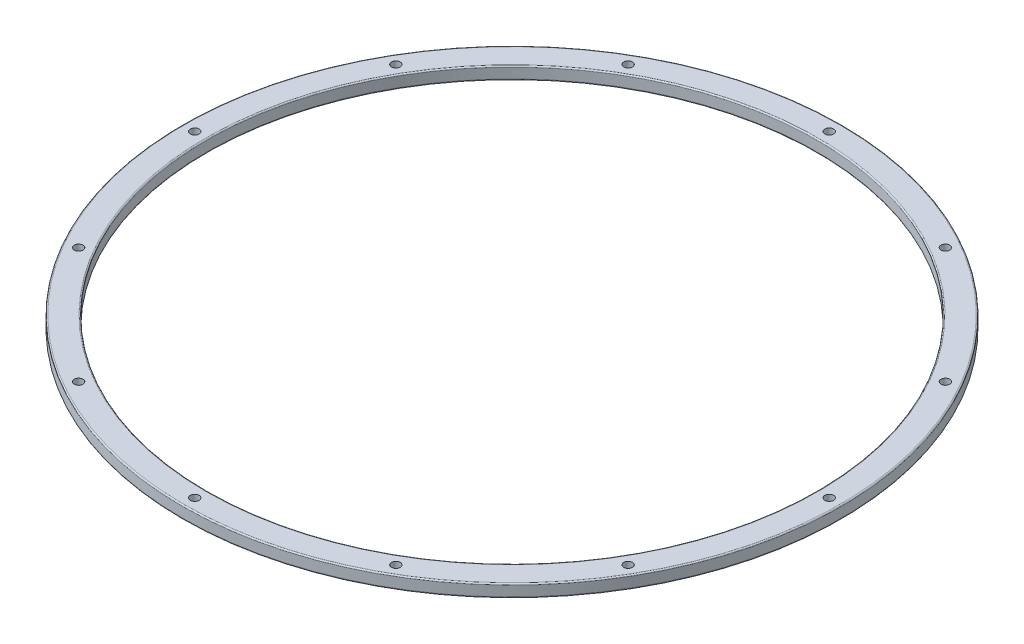
SolidWorks part; units mm, degrees
material "PTFE (general)"
ref_plane "Front Plane" through (0, 0, 0) normal (0, 0, 1) x (1, 0, 0)
ref_plane "Top Plane" through (0, 0, 0) normal (0, 1, 0) x (1, 0, 0)
ref_plane "Right Plane" through (0, 0, 0) normal (1, 0, 0) x (0, 0, -1)
ref_axis "Axis1" through (0, 55, 0) along (0, -1, 0)
sketch "Sketch1" plane through (0, 0, 0) normal (0, 0, 1) x (1, 0, 0)
  line L0 (-76.2, 0) -> (0, 0) construction
  line L1 (-76.5175, 0) -> (-82.042, 0)
  line L2 (-76.2, 0.3175) -> (-76.2, 2.8575)
  line L3 (-76.5175, 3.175) -> (-82.042, 3.175)
  line L4 (-82.3595, 0.3175) -> (-82.3595, 2.8575)
  line L5 (0, 55) -> (0, -55) construction
  arc A0 (-82.042, 3.175) -> (-82.3595, 2.8575) centre (-82.042, 2.8575) ccw
  arc A1 (-82.042, 0) -> (-82.3595, 0.3175) centre (-82.042, 0.3175) cw
  arc A2 (-76.5175, 0) -> (-76.2, 0.3175) centre (-76.5175, 0.3175) ccw
  arc A3 (-76.2, 2.8575) -> (-76.5175, 3.175) centre (-76.5175, 2.8575) ccw
  point P12 (-82.3595, 0)
  point P18 (-76.2, 3.175)
  dimension "D4" = 0.3175
  dimension "D1" = 3.175
  dimension "D2" = 6.1595
  dimension "D3" = 76.2
revolve "Main" add sketch "Sketch1" angle 360 about axis through (0, 55, 0) along (0, -1, 0)
sketch "Hole Location" plane through (0, 0, 0) normal (0, 1, 0) x (1, 0, 0)
  line L0 (0, 0) -> (-79.2797, 0) construction
  circle A0 centre (0, 0) radius 79.2797 construction
  dimension "D1" = 158.5595
hole_wizard "#44 (0.086) Diameter Hole1" positions "Sketch3" profile "Sketch5" hole size "#44" standard "ANSI Inch" end condition through all
sketch "Sketch3" plane through (0, 0, 0) normal (0, -1, 0) x (-1, 0, 0)
  point P0 (79.2797, 0)
sketch "Sketch5" plane through (-79.2797, 0, 0) normal (1, 0, 0) x (0, 0, -1)
  line L0 (0, 0) -> (0, 3.175)
  line L1 (0, 3.175) -> (1.0922, 3.175)
  line L2 (1.0922, 3.175) -> (1.0922, 0)
  line L5 (1.0922, 0) -> (0, 0)
  line L11 (0, -6.35) -> (0, 107.95) construction
  dimension "Thru Hole Dia." = 2.1844
  dimension "Thru Hole Depth" = 3.175
pattern_circular "Screw Passthroughs" count 12 over 360 about axis through (0, 0, 0) along (0, 1, 0) of "#44 (0.086) Diameter Hole1"
